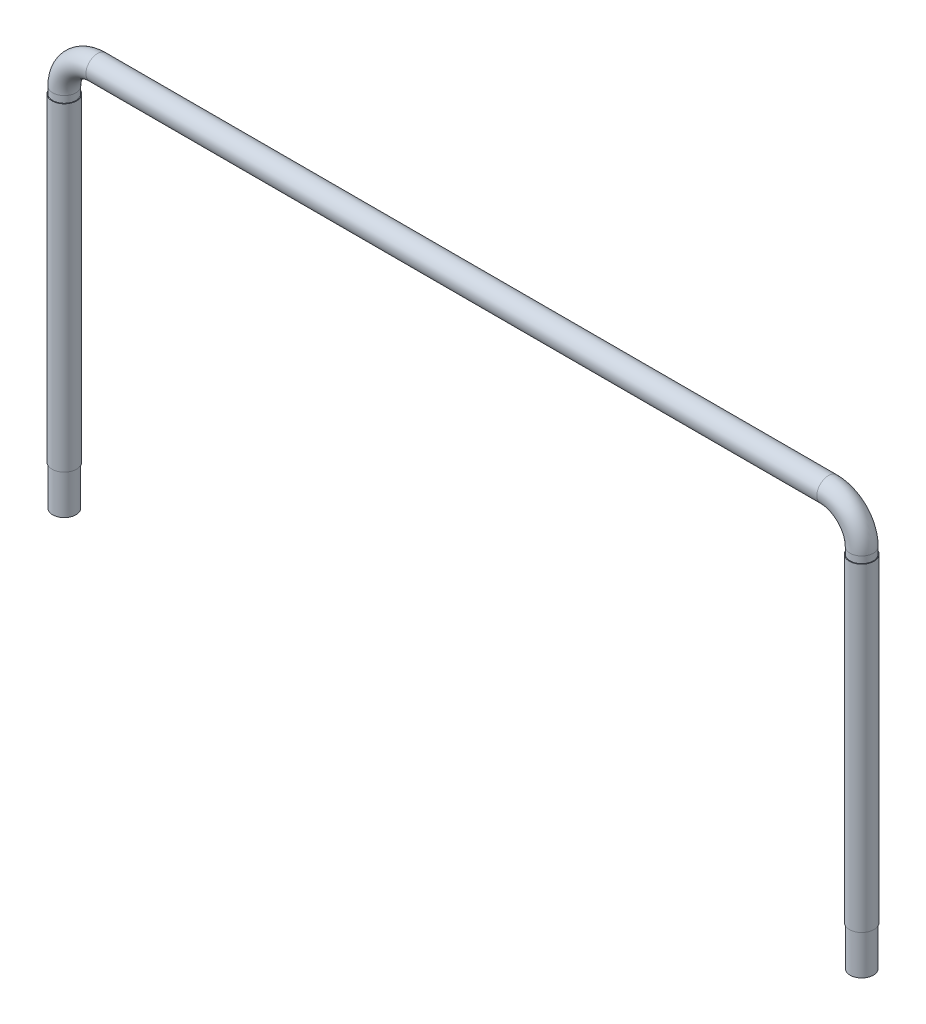
SolidWorks part; units mm, degrees
ref_plane "Front Plane" through (0, 0, 0) normal (0, 0, 1) x (1, 0, 0)
ref_plane "Top Plane" through (0, 0, 0) normal (0, 1, 0) x (1, 0, 0)
ref_plane "Right Plane" through (0, 0, 0) normal (1, 0, 0) x (0, 0, -1)
sketch "Sketch1" plane through (0, 0, 0) normal (0, 0, 1) x (1, 0, 0)
  line L0 (-1524, 0) -> (-1524, 1397)
  line L1 (-1397, 1524) -> (1397, 1524)
  line L2 (1524, 1397) -> (1524, 0)
  line L3 (0, 0) -> (0, 1524) construction
  arc A0 (1397, 1524) -> (1524, 1397) centre (1397, 1397) cw
  arc A1 (-1524, 1397) -> (-1397, 1524) centre (-1397, 1397) cw
  point P9 (1524, 1524)
  point P12 (-1524, 1524)
  dimension "D3" = 127
  dimension "D1" = 3048
  dimension "D2" = 1524
sketch "Sketch2" plane through (0, 0, 0) normal (0, 1, 0) x (1, 0, 0)
  circle A0 centre (-1524, 0) radius 44.45
  dimension "D1" = 88.9
sweep "Sweep1" add profiles "Sketch2" path "Sketch1"
ref_plane "Plane1" through (0, 152.4, 0) normal (0, -1, 0) x (-1, 0, 0)
sketch "Sketch3" plane through (0, 152.4, 0) normal (0, -1, 0) x (-1, 0, 0)
  circle A0 centre (-1524, 0) radius 44.45 construction
  circle A1 centre (1524, 0) radius 44.45 construction
  circle A2 centre (-1524, 0) radius 44.45 construction
  circle A3 centre (1524, 0) radius 44.45 construction
  circle A4 centre (-1524, 0) radius 46.99
  circle A5 centre (1524, 0) radius 46.99
  dimension "D1" = 2.54
extrude "Boss-Extrude1" add sketch "Sketch3" against normal blind 1219.2
